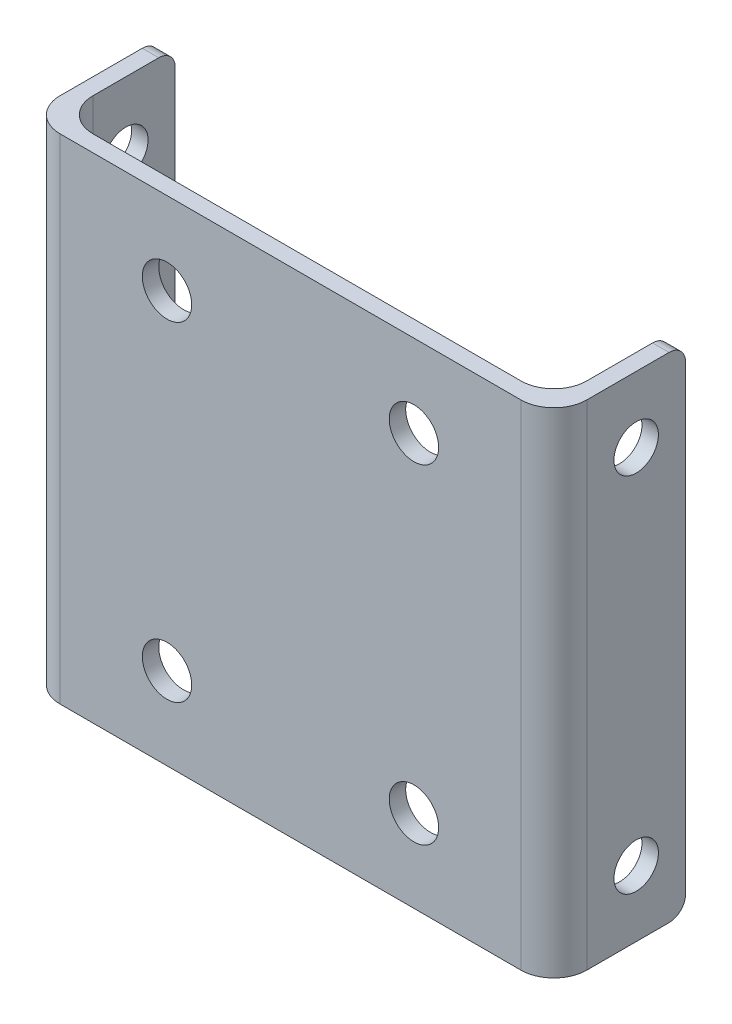
SolidWorks part; units mm, degrees
material "1060 Alloy"
ref_plane "Front Plane" through (0, 0, 0) normal (0, 0, 1) x (1, 0, 0)
ref_plane "Top Plane" through (0, 0, 0) normal (0, 1, 0) x (1, 0, 0)
ref_plane "Right Plane" through (0, 0, 0) normal (1, 0, 0) x (0, 0, -1)
sketch "Sketch1" plane through (0, 0, 0) normal (0, 1, 0) x (1, 0, 0)
  line L1 (-21.5, 0.5) -> (8.5, 0.5)
  line L2 (-22.5, 0.5) -> (-22.5, -0.5)
  line L3 (-22.5, -0.5) -> (9.5, -0.5)
  line L4 (9.5, 0.5) -> (9.5, -0.5)
  line L8 (9.5, 0.5) -> (9.5, 7.5)
  line L9 (9.5, 7.5) -> (8.5, 7.5)
  line L10 (8.5, 0.5) -> (8.5, 7.5)
  line L12 (-22.5, 0.5) -> (-22.5, 7.5)
  line L13 (-22.5, 7.5) -> (-21.5, 7.5)
  line L14 (-21.5, 0.5) -> (-21.5, 7.5)
  point P0 (0, 0)
  dimension "D1" = 32
  dimension "D2" = 1
  dimension "D3" = 1
  dimension "D4" = 1
  dimension "D5" = 7
  dimension "D6" = 7
  dimension "D7" = 1
extrude "Boss-Extrude1" add sketch "Sketch1" along normal blind 30
fillet "Fillet2" radius 2 4 edges at (-22.5, 15, 0.5) (-21.5, 15, -0.5) (9.5, 15, 0.5) (8.5, 15, -0.5)
sketch "Sketch3" plane through (0, 0, 0.5) normal (0, 0, 1) x (1, 0, 0)
  line L0 (-6.5, 25) -> (-14, 25)
  line L1 (-6.5, 25) -> (1, 25)
  line L2 (-6.5, 30) -> (-6.5, 25)
  line L3 (-20.5, 30) -> (7.5, 30) construction
  line L6 (-6.5, 0) -> (-6.5, 5)
  line L7 (-20.5, 0) -> (7.5, 0) construction
  line L8 (-6.5, 5) -> (-14, 5)
  line L9 (-6.5, 5) -> (1, 5)
  circle A0 centre (-14, 25) radius 1.5
  circle A1 centre (1, 25) radius 1.5
  circle A2 centre (-14, 5) radius 1.5
  circle A3 centre (1, 5) radius 1.5
  dimension "D3" = 7.5
  dimension "D4" = 3
  dimension "D9" = 3
  dimension "D10" = 3
  dimension "D5" = 3
  dimension "D2" = 7.5
  dimension "D6" = 5
  dimension "D7" = 7.5
  dimension "D8" = 7.5
  dimension "D11" = 5
extrude "Cut-Extrude4" cut sketch "Sketch3" against normal through all
sketch "Sketch4" plane through (9.5, 0, 0) normal (1, 0, 0) x (0, 0, -1)
  line L0 (4.5, 30) -> (4.5, 26)
  line L2 (1.5, 30) -> (7.5, 30) construction
  line L6 (4.5, 0) -> (4.5, 4)
  line L10 (1.5, 0) -> (7.5, 0) construction
  circle A0 centre (4.5, 26) radius 1.35
  circle A1 centre (4.5, 4) radius 1.35
  dimension "D3" = 2.7
  dimension "D4" = 2.7
  dimension "D1" = 4
  dimension "D2" = 4
extrude "Cut-Extrude3" cut sketch "Sketch4" against normal through all
fillet "Fillet3" radius 1 4 edges at (-22, 30, -7.5) (-22, 0, -7.5) (9, 0, -7.5) (9, 30, -7.5)
